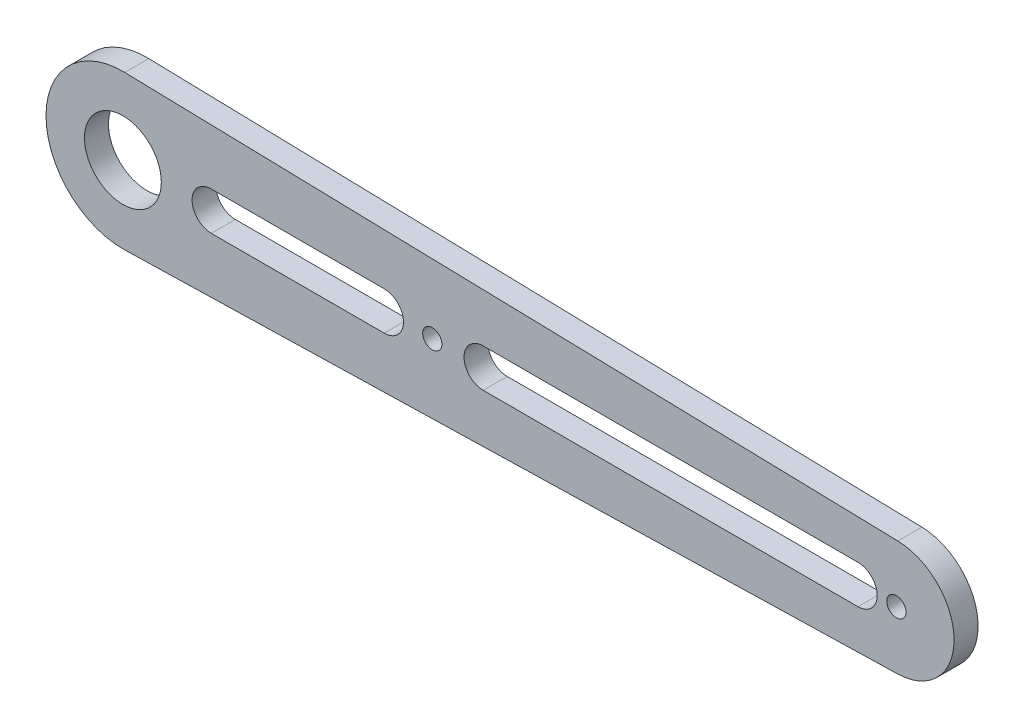
SolidWorks part; units mm, degrees
material "Thornel Mat VMA"
ref_plane "前视基准面" through (0, 0, 0) normal (0, 0, 1) x (1, 0, 0)
ref_plane "上视基准面" through (0, 0, 0) normal (0, 1, 0) x (1, 0, 0)
ref_plane "右视基准面" through (0, 0, 0) normal (1, 0, 0) x (0, 0, -1)
sketch "草图1" plane through (0, 0, 0) normal (0, 0, 1) x (1, 0, 0)
  line L2 (0.3975, -15.9951) -> (161.2981, -11.9963)
  line L3 (161.2981, 11.9963) -> (0.3975, 15.9951)
  line L6 (0, 0) -> (64.4, 0) construction
  line L103 (18.4, 0) -> (54.4, 0) construction
  line L104 (18.4, 4) -> (54.4, 4)
  line L105 (18.4, -4) -> (54.4, -4)
  line L106 (75, 0) -> (153, 0) construction
  line L107 (75, 4) -> (153, 4)
  line L108 (75, -4) -> (153, -4)
  circle A0 centre (0, 0) radius 8
  arc A2 (0.3975, 15.9951) -> (0.3975, -15.9951) centre (0, 0) ccw
  arc A4 (161.2981, -11.9963) -> (161.2981, 11.9963) centre (161, 0) ccw
  circle A5 centre (161, 0) radius 2
  arc A39 (18.4, 4) -> (18.4, -4) centre (18.4, 0) ccw
  arc A40 (54.4, -4) -> (54.4, 4) centre (54.4, 0) ccw
  arc A41 (75, 4) -> (75, -4) centre (75, 0) ccw
  arc A42 (153, -4) -> (153, 4) centre (153, 0) ccw
  circle A62 centre (64.4, 0) radius 2
  point P21 (36.4, 0)
  point P124 (114, 0)
  dimension "D2" = 16
  dimension "D3" = 16
  dimension "D7" = 12
  dimension "D9" = 4
  dimension "D11" = 64.4
  dimension "D6" = 4
  dimension "D10" = 4
  dimension "D12" = 4
  dimension "D8" = 161
  dimension "D13" = 36
  dimension "D17" = 8
  dimension "D19" = 10
  dimension "D20" = 78
extrude "凸台-拉伸1" add sketch "草图1" along normal blind 5
